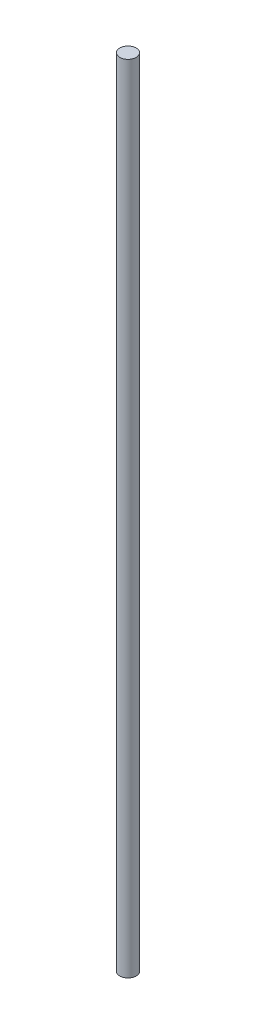
SolidWorks part; units mm, degrees
material "201 Annealed Stainless Steel (SS)"
ref_plane "Front Plane" through (0, 0, 0) normal (0, 0, 1) x (1, 0, 0)
ref_plane "Top Plane" through (0, 0, 0) normal (0, 1, 0) x (1, 0, 0)
ref_plane "Right Plane" through (0, 0, 0) normal (1, 0, 0) x (0, 0, -1)
sketch "Sketch1" plane through (0, 0, 0) normal (0, 1, 0) x (1, 0, 0)
  circle A0 centre (0, 0) radius 3
extrude "Boss-Extrude1" add sketch "Sketch1" along normal blind 292
